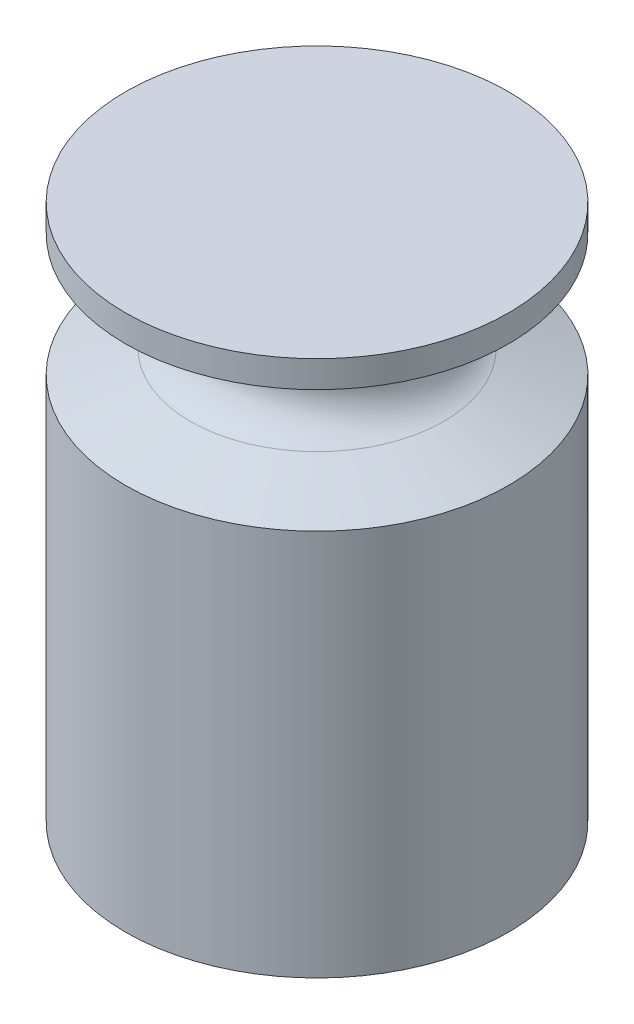
SolidWorks part; units mm, degrees
material "AISI 1020"
ref_plane "Front Plane" through (0, 0, 0) normal (0, 0, 1) x (1, 0, 0)
ref_plane "Top Plane" through (0, 0, 0) normal (0, 1, 0) x (1, 0, 0)
ref_plane "Right Plane" through (0, 0, 0) normal (1, 0, 0) x (0, 0, -1)
sketch "Sketch1" plane through (0, 0, 0) normal (0, 1, 0) x (1, 0, 0)
  circle A0 centre (0, 0) radius 25
  dimension "D1" = 50
extrude "Boss-Extrude1" add sketch "Sketch1" along normal blind 70
sketch "Sketch2" plane through (0, 0, 0) normal (1, 0, 0) x (0, 0, -1)
  line L0 (25, 50.5) -> (16.533, 53.5)
  line L1 (25, 66.5) -> (16.533, 63.5)
  line L2 (25, 0) -> (25, 70) construction
  line L3 (25, 58.5) -> (13, 58.5) construction
  line L4 (25, 70) -> (-25, 70) construction
  line L5 (25, 66.5) -> (25, 50.5)
  arc A0 (16.533, 63.5) -> (13, 58.5) centre (18.3046, 58.5) ccw
  arc A1 (16.533, 53.5) -> (13, 58.5) centre (18.3046, 58.5) cw
  dimension "D1" = 3.5
  dimension "D2" = 12
  dimension "D3" = 8
  dimension "D4" = 10
ref_axis "Axis1" through (0, 73.5, 0) along (0, -1, 0)
revolve "Cut-Revolve1" cut sketch "Sketch2" angle 360 about axis through (0, 73.5, 0) along (0, -1, 0)
